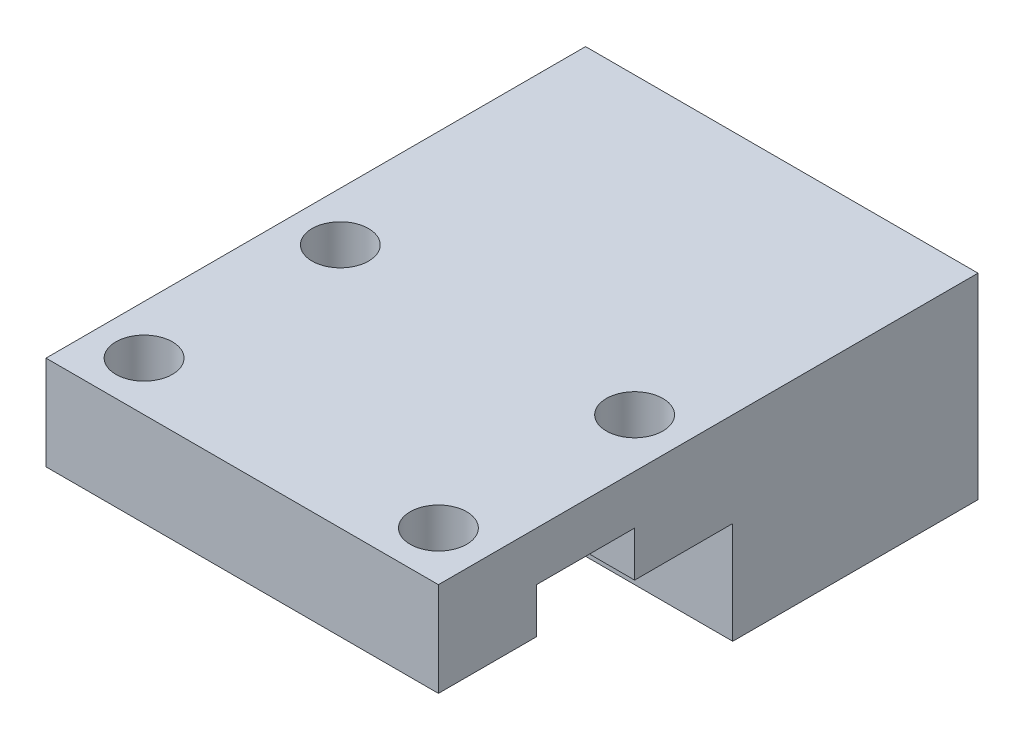
SolidWorks part; units mm, degrees
ref_plane "Front Plane" through (0, 0, 0) normal (0, 0, 1) x (1, 0, 0)
ref_plane "Top Plane" through (0, 0, 0) normal (0, 1, 0) x (1, 0, 0)
ref_plane "Right Plane" through (0, 0, 0) normal (1, 0, 0) x (0, 0, -1)
sketch "Sketch1" plane through (0, 0, 0) normal (1, 0, 0) x (0, 0, -1)
  line L0 (9.525, -0.254) -> (9.525, 0) construction
  line L1 (0, 0) -> (19.05, 0)
  line L2 (0, 0) -> (0, 6.096)
  line L3 (0, 6.096) -> (34.925, 6.096)
  line L4 (34.925, -6.604) -> (34.925, 6.096)
  line L5 (9.525, 2.921) -> (9.525, 6.096) construction
  line L6 (19.05, 0) -> (19.05, -6.604)
  line L7 (12.7, 2.921) -> (6.35, 2.921)
  line L8 (6.35, 2.921) -> (6.35, -3.429)
  line L9 (6.35, -3.429) -> (12.7, -3.429)
  line L10 (12.7, -3.429) -> (12.7, 2.921)
  line L11 (19.05, -6.604) -> (34.925, -6.604)
  circle A1 centre (9.525, -0.254) radius 3.175 construction
  dimension "D1" = 6.35
  dimension "D2" = 0.254
  dimension "D3" = 25.4
  dimension "D4" = 3.175
  dimension "D5" = 9.525
  dimension "D6" = 9.525
  dimension "D7" = 12.7
extrude "Boss-Extrude1" add sketch "Sketch1" along normal blind 25.4
sketch "Sketch2" plane through (0, 0, -34.925) normal (0, 0, -1) x (-1, 0, 0)
  line L0 (-19.05, 2.921) -> (-25.4, 2.921) construction
  line L1 (-6.35, 2.921) -> (0, 2.921) construction
  line L2 (-19.05, -3.429) -> (-25.4, -3.429) construction
  line L3 (-6.35, -3.429) -> (0, -3.429) construction
  line L4 (-25.4, -6.604) -> (-25.4, 6.096) construction
  line L5 (0, -6.604) -> (0, 6.096) construction
  line L6 (-25.4, -6.604) -> (0, -6.604) construction
  circle A0 centre (-19.05, 2.921) radius 1.8288
  circle A1 centre (-6.35, 2.921) radius 1.8288
  circle A2 centre (-19.05, -3.429) radius 1.8288
  circle A3 centre (-6.35, -3.429) radius 1.8288
  dimension "D5" = 3.6576
  dimension "D1" = 6.35
  dimension "D2" = 6.35
  dimension "D3" = 6.35
  dimension "D4" = 3.175
  dimension "D6" = 12.7
extrude "Cut-Extrude1" cut sketch "Sketch2" against normal blind 12.7
sketch "Sketch3" plane through (0, 0, 0) normal (0, -1, 0) x (1, 0, 0)
  line L0 (0, 0) -> (0, -6.35) construction
  line L1 (3.175, -3.175) -> (3.175, 0) construction
  line L2 (25.4, 0) -> (0, 0) construction
  line L3 (3.175, -3.175) -> (3.175, -6.35) construction
  line L4 (25.4, -6.35) -> (0, -6.35) construction
  line L5 (3.175, -15.875) -> (3.175, -12.7) construction
  line L6 (25.4, -12.7) -> (0, -12.7) construction
  line L7 (3.175, -15.875) -> (3.175, -19.05) construction
  line L8 (25.4, -19.05) -> (0, -19.05) construction
  line L9 (22.225, -3.175) -> (22.225, 0) construction
  line L10 (22.225, -3.175) -> (22.225, -6.35) construction
  line L11 (22.225, -15.875) -> (22.225, -12.7) construction
  line L12 (22.225, -15.875) -> (22.225, -19.05) construction
  line L13 (25.4, -19.05) -> (0, -19.05) construction
  line L14 (25.4, -12.7) -> (0, -12.7) construction
  line L15 (25.4, 0) -> (25.4, -6.35) construction
  circle A0 centre (3.175, -3.175) radius 1.8288
  circle A1 centre (3.175, -15.875) radius 1.8288
  circle A2 centre (22.225, -3.175) radius 1.8288
  circle A3 centre (22.225, -15.875) radius 1.8288
  dimension "D1" = 3.6576
  dimension "D2" = 3.6576
  dimension "D4" = 3.6576
  dimension "D5" = 3.6576
  dimension "D3" = 3.175
  dimension "D6" = 3.175
  dimension "D7" = 12.7
  dimension "D8" = 19.05
extrude "Cut-Extrude2" cut sketch "Sketch3" against normal blind 12.7
